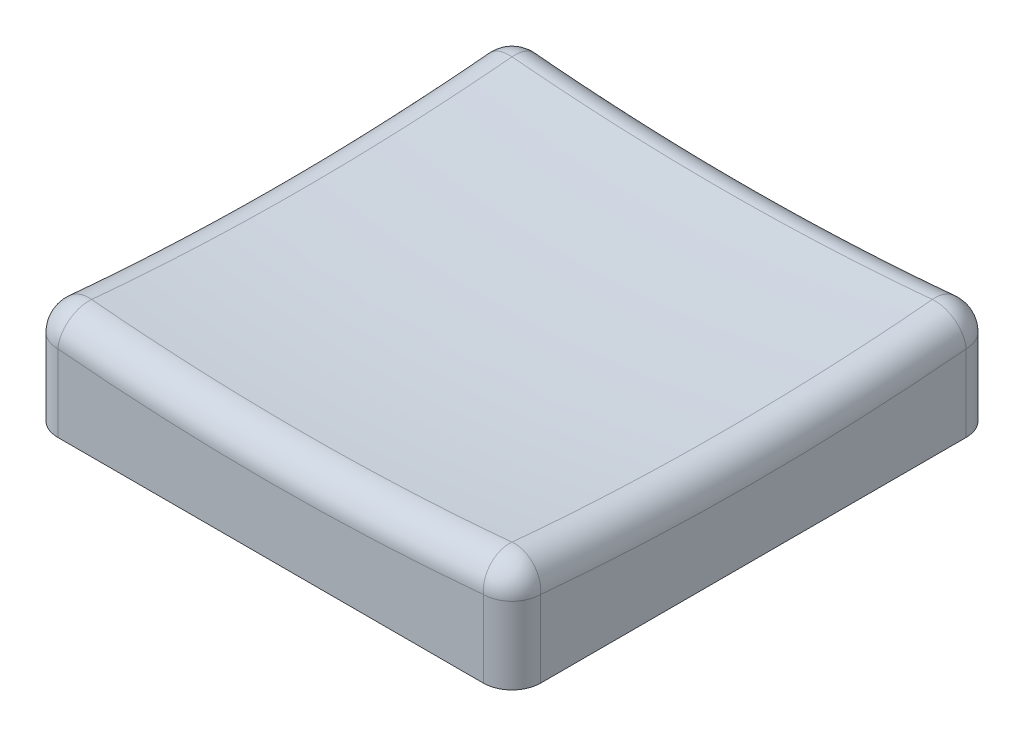
SolidWorks part; units mm, degrees
ref_plane "前视基准面" through (0, 0, 0) normal (0, 0, 1) x (1, 0, 0)
ref_plane "上视基准面" through (0, 0, 0) normal (0, 1, 0) x (1, 0, 0)
ref_plane "右视基准面" through (0, 0, 0) normal (1, 0, 0) x (0, 0, -1)
sketch "草图1" plane through (0, 0, 0) normal (0, 1, 0) x (1, 0, 0)
  line L1 (-8.425, 8.425) -> (8.425, 8.425)
  line L2 (-8.425, 8.425) -> (-8.425, -8.425)
  line L3 (-8.425, -8.425) -> (8.425, -8.425)
  line L4 (8.425, 8.425) -> (8.425, -8.425)
  line L5 (-8.425, 8.425) -> (8.425, -8.425) construction
  line L6 (-8.425, -8.425) -> (8.425, 8.425) construction
  point P0 (0, 0)
  dimension "D1" = 16.85
  dimension "D2" = 16.85
extrude "凸台-拉伸1" add sketch "草图1" along normal blind 4
shell "抽壳1" thickness 1.5
sketch "草图2" plane through (0, 0, 0) normal (0, 0, 1) x (1, 0, 0)
  line L0 (-6.925, 0) -> (6.925, 0) construction
  line L2 (0, 164) -> (0, 3)
  arc A0 (0, 3) -> (0, 164) centre (0, 83.5) ccw
  dimension "D1" = 83.5
  dimension "D3" = 161
  dimension "D2" = 0
revolve "切除-旋转5" cut sketch "草图2" angle 360 about L0
sketch "草图3" plane through (0, 0, 0) normal (0, 0, 1) x (1, 0, 0)
  line L0 (0, 0) -> (0, 49.6085) construction
  dimension "D1" = 0
fillet "圆角1" radius 1 8 edges at (8.425, 1.9433, 8.425) (8.425, 3.4421, 0) (8.425, 1.9433, -8.425) (0, 3.4421, -8.425) (-8.425, 1.9433, -8.425) (-8.425, 1.9433, 8.425) (0, 3.4421, 8.425) (-8.425, 3.4421, 0)
